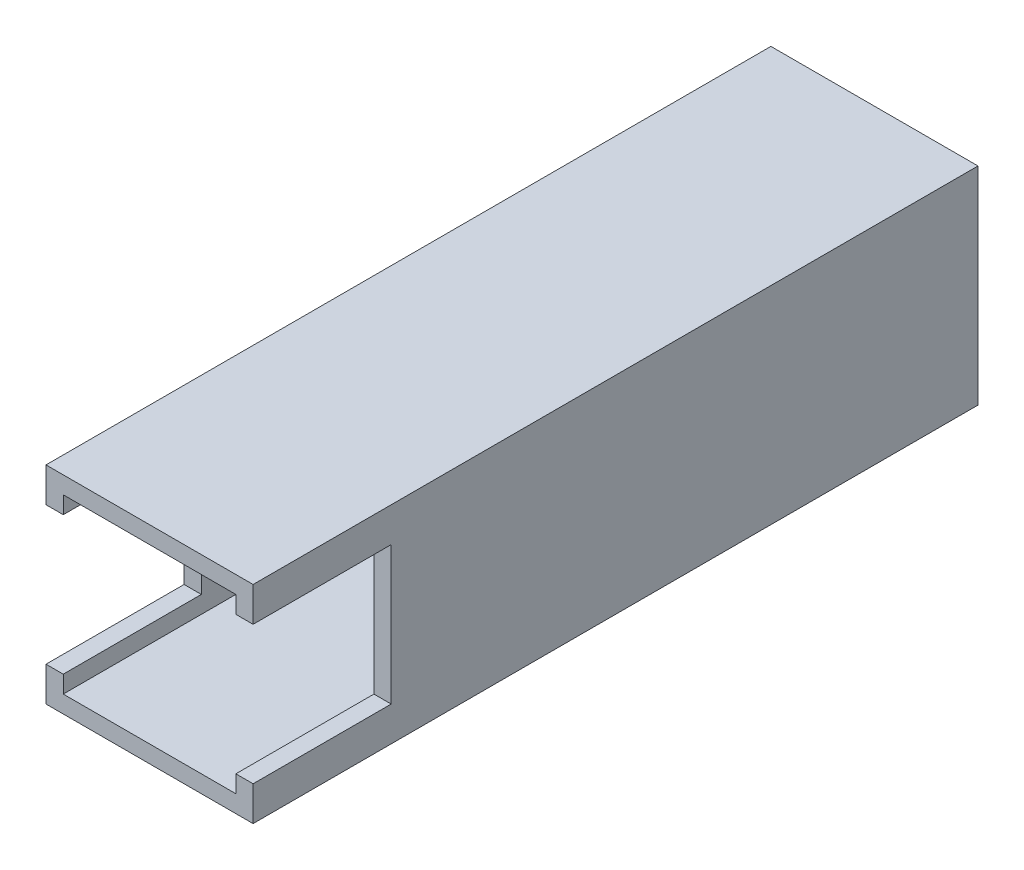
SolidWorks part; units mm, degrees
material "Titanium"
ref_plane "Front Plane" through (0, 0, 0) normal (0, 0, 1) x (1, 0, 0)
ref_plane "Top Plane" through (0, 0, 0) normal (0, 1, 0) x (1, 0, 0)
ref_plane "Right Plane" through (0, 0, 0) normal (1, 0, 0) x (0, 0, -1)
sketch "Sketch1" plane through (0, 0, 0) normal (0, 1, 0) x (1, 0, 0)
  line L1 (-19.05, 66.675) -> (19.05, 66.675)
  line L2 (-19.05, 66.675) -> (-19.05, -66.675)
  line L3 (-19.05, -66.675) -> (19.05, -66.675)
  line L4 (19.05, 66.675) -> (19.05, -66.675)
  dimension "D1" = 19.05
  dimension "D2" = 19.05
  dimension "D3" = 66.675
  dimension "D4" = 66.675
extrude "Boss-Extrude1" add sketch "Sketch1" along normal mid plane 38.1
sketch "Sketch2" plane through (0, 0, 66.675) normal (0, 0, 1) x (1, 0, 0)
  line L0 (-19.05, 19.05) -> (-19.05, -19.05) construction
  line L1 (-15.875, 15.875) -> (15.875, 15.875)
  line L2 (-15.875, 15.875) -> (-15.875, -15.875)
  line L3 (-15.875, -15.875) -> (15.875, -15.875)
  line L4 (15.875, 15.875) -> (15.875, -15.875)
  line L5 (19.05, 19.05) -> (19.05, -19.05) construction
  line L6 (-19.05, -19.05) -> (19.05, -19.05) construction
  line L7 (-19.05, 19.05) -> (19.05, 19.05) construction
  dimension "D1" = 3.175
  dimension "D2" = 3.175
  dimension "D3" = 3.175
  dimension "D4" = 3.175
extrude "Cut-Extrude1" cut sketch "Sketch2" against normal through all
sketch "Sketch3" plane through (19.05, 0, 0) normal (1, 0, 0) x (0, 0, -1)
  line L0 (-66.675, 19.05) -> (-66.675, -19.05) construction
  line L1 (-66.675, 12.7) -> (-41.275, 12.7)
  line L2 (-66.675, 12.7) -> (-66.675, -12.7)
  line L3 (-66.675, -12.7) -> (-41.275, -12.7)
  line L4 (-41.275, 12.7) -> (-41.275, -12.7)
  line L5 (-66.675, -19.05) -> (66.675, -19.05) construction
  line L6 (-66.675, 19.05) -> (66.675, 19.05) construction
  dimension "D1" = 25.4
  dimension "D2" = 6.35
  dimension "D3" = 6.35
extrude "Cut-Extrude2" cut sketch "Sketch3" against normal through all
